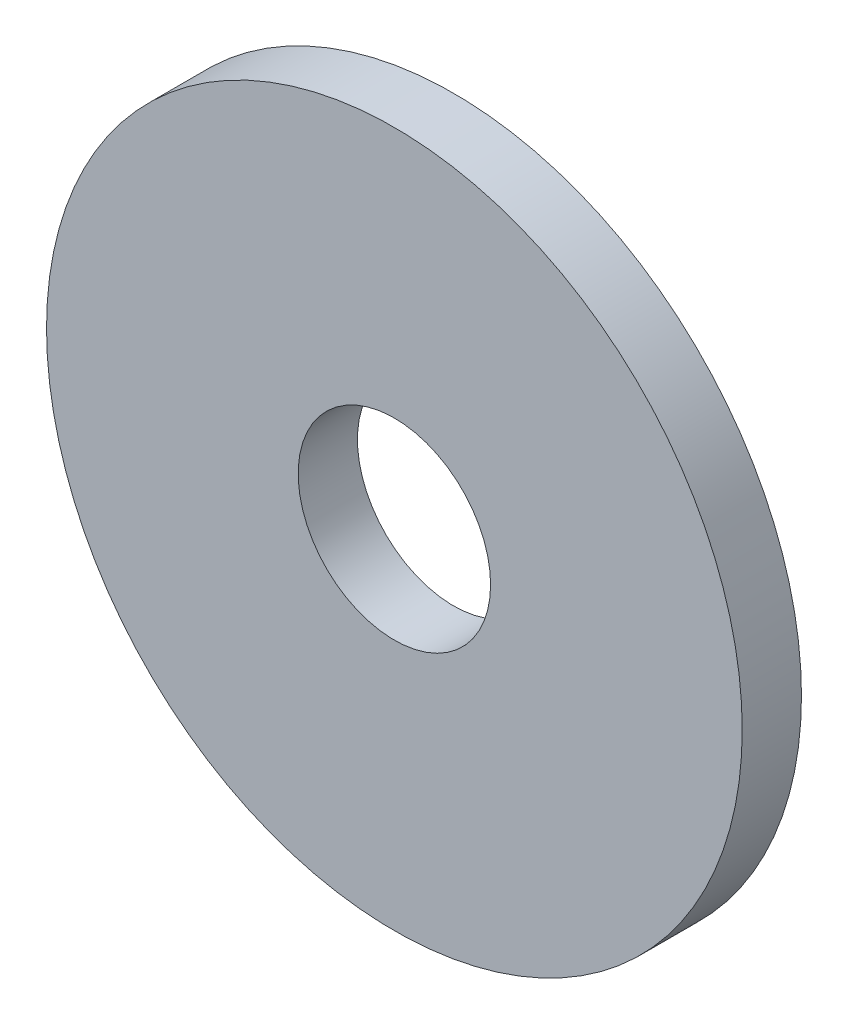
SolidWorks part; units mm, degrees
material "Nylon 101"
ref_plane "Front Plane" through (0, 0, 0) normal (0, 0, 1) x (1, 0, 0)
ref_plane "Top Plane" through (0, 0, 0) normal (0, 1, 0) x (1, 0, 0)
ref_plane "Right Plane" through (0, 0, 0) normal (1, 0, 0) x (0, 0, -1)
sketch "Sketch1" plane through (0, 0, 0) normal (0, 0, 1) x (1, 0, 0)
  line L0 (0, 0) -> (1.823, -1.823) construction
  line L1 (-2.5781, 0) -> (2.5781, 0)
  line L2 (-9.3218, 0) -> (9.3218, 0) construction
  circle A0 centre (0, 0) radius 2.5781 construction
  circle A1 centre (0, 0) radius 9.3218 construction
  circle A2 centre (0, 0) radius 2.413 construction
  point P0 (0, 0)
  point P7 (1.823, -1.823)
  dimension "D1" = 45
  dimension "ID" = 5.1562
  dimension "OD" = 18.6436
  dimension "For Screw Size" = 4.826
sketch "Sketch2" plane through (0, 0, 0) normal (1, 0, 0) x (0, 0, -1)
  line L0 (0, 9.3218) -> (0, -9.3218) construction
  line L1 (-0.8064, -9.3218) -> (0.8065, -9.3218) construction
  line L2 (-0.8064, -9.3218) -> (-0.8065, 9.3218) construction
  line L3 (-0.8065, 9.3218) -> (0.8065, 9.3218) construction
  line L4 (0.8065, -9.3218) -> (0.8065, 9.3218) construction
  line L5 (0, 9.3218) -> (0, -9.3218) construction
  line L6 (-0.8064, 0) -> (0.8064, 0) construction
  point P0 (0, 0)
  dimension "Thickness Range" = 1.6129
sketch "Sketch3" plane through (0, 0, 0) normal (0, 0, 1) x (1, 0, 0)
  circle A0 centre (0, 0) radius 9.3218 construction
  circle A1 centre (0, 0) radius 2.5781 construction
  circle A2 centre (0, 0) radius 9.3218
  circle A3 centre (0, 0) radius 2.5781
extrude "Boss-Extrude1" add sketch "Sketch3" along normal mid plane 1.5875
